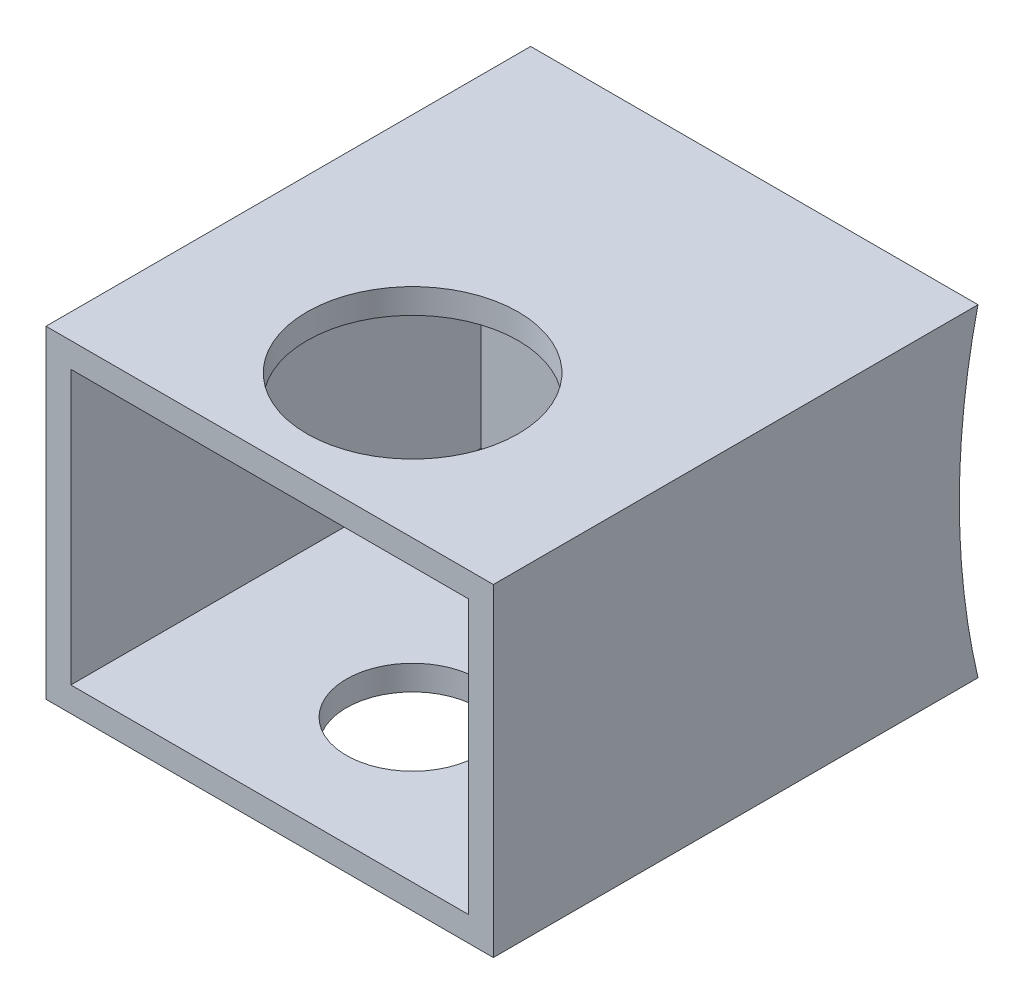
SolidWorks part; units mm, degrees
ref_plane "Front Plane" through (0, 0, 0) normal (0, 0, 1) x (1, 0, 0)
ref_plane "Top Plane" through (0, 0, 0) normal (0, 1, 0) x (1, 0, 0)
ref_plane "Right Plane" through (0, 0, 0) normal (1, 0, 0) x (0, 0, -1)
sketch "Sketch1" plane through (0, 0, 0) normal (0, 0, 1) x (1, 0, 0)
  line L0 (-7.8396, 5.0428) -> (-7.8396, -1.5612)
  line L1 (-7.8396, -1.5612) -> (1.3044, -1.5612)
  line L2 (1.3044, -1.5612) -> (1.3044, 5.0428)
  line L3 (1.3044, 5.0428) -> (-7.8396, 5.0428)
  dimension "D1" = 6.604
  dimension "D2" = 9.144
extrude "Boss-Extrude1" add sketch "Sketch1" along normal blind 9.906
sketch "Sketch4" plane through (0, 0, 9.906) normal (0, 0, 1) x (1, 0, 0)
  line L0 (-7.3316, 4.5348) -> (-7.3316, -1.0532)
  line L1 (-7.3316, -1.0532) -> (0.7964, -1.0532)
  line L2 (0.7964, -1.0532) -> (0.7964, 4.5348)
  line L3 (0.7964, 4.5348) -> (-7.3316, 4.5348)
  line L4 (-7.8396, 5.0428) -> (-7.8396, -1.5612) construction
  line L5 (1.3044, -1.5612) -> (1.3044, 5.0428) construction
  line L6 (1.3044, 5.0428) -> (-7.8396, 5.0428) construction
  line L7 (-7.8396, -1.5612) -> (1.3044, -1.5612) construction
  dimension "D1" = 0.508
  dimension "D2" = 0.508
  dimension "D3" = 0.508
  dimension "D4" = 0.508
extrude "Cut-Extrude1" cut sketch "Sketch4" against normal blind 8.382
sketch "Sketch7" plane through (-7.8396, 0, 0) normal (-1, 0, 0) x (0, 0, 1)
  line L0 (0, -1.5612) -> (-14.0964, 1.7408) construction
  line L1 (-14.0964, 1.7408) -> (0, 5.0428) construction
  dimension "D1" = 14.478
  dimension "D2" = 14.478
sketch "Sketch8" plane through (-7.8396, 0, 0) normal (-1, 0, 0) x (0, 0, 1)
  line L0 (0, 5.0428) -> (0, -1.5612) construction
  line L1 (0, 5.0428) -> (0, -1.5612)
  arc A0 (0, -1.5612) -> (0, 5.0428) centre (-14.0964, 1.7408) ccw
extrude "Cut-Extrude2" cut sketch "Sketch8" against normal through all
ref_plane "Plane1" through (-3.2676, 0, 0) normal (-1, 0, 0) x (0, 0, 1)
ref_plane "Plane2" through (0, 1.7408, 0) normal (0, 1, 0) x (1, 0, 0)
sketch "Sketch9" plane through (0, 5.0428, 0) normal (0, 1, 0) x (1, 0, 0)
  line L0 (-3.2676, 3.6322) -> (-3.2676, -3.6322) construction
  line L1 (1.3044, -9.906) -> (-7.8396, -9.906) construction
  point P0 (-3.2676, -6.985)
  point P5 (0, 0)
  point P6 (0, 0)
  dimension "D1" = 2.921
sketch "Sketch11" plane through (0, 5.0428, 0) normal (0, 1, 0) x (1, 0, 0)
  circle A0 centre (-3.2676, -6.985) radius 2.159
extrude "Cut-Extrude4" cut sketch "Sketch11" against normal up to next contours A0
hole_wizard "#6-32 Tapped Hole4" positions "Sketch18" profile "Sketch19" tap size "#6-32" standard "ANSI Inch" end condition up to next
sketch "Sketch18" plane through (0, -1.5612, 0) normal (0, -1, 0) x (-1, 0, 0)
  point P0 (3.2676, -6.985)
sketch "Sketch19" plane through (-3.2676, -1.5612, 6.985) normal (1, 0, 0) x (0, 0, -1)
  line L0 (0, 0) -> (0, 0.508)
  line L1 (0, 0.508) -> (1.3525, 0.508)
  line L2 (1.3525, 0.508) -> (1.3525, 0)
  line L5 (1.3525, 0) -> (0, 0)
  line L11 (0, -6.35) -> (0, 107.95) construction
  dimension "Thread Major Dia." = 2.7051
  dimension "Thru Tap Drill Depth" = 0.508
